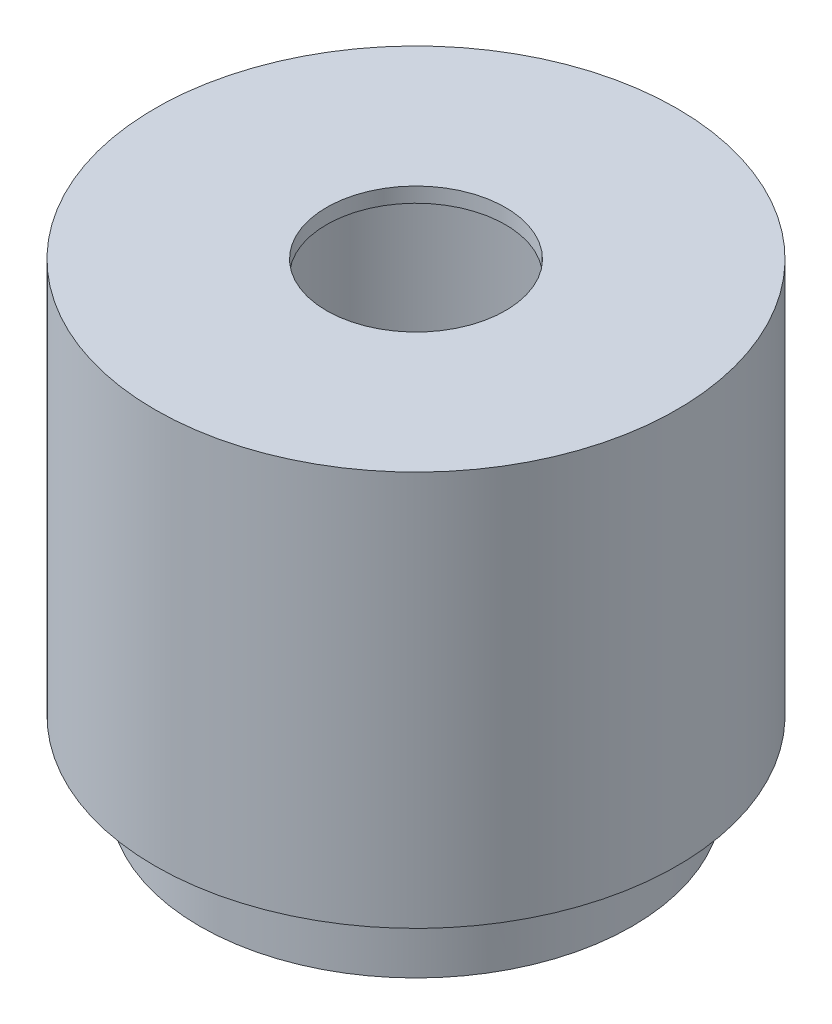
SolidWorks part; units mm, degrees
material "1060 Alloy"
ref_plane "Front Plane" through (0, 0, 0) normal (0, 0, 1) x (1, 0, 0)
ref_plane "Top Plane" through (0, 0, 0) normal (0, 1, 0) x (1, 0, 0)
ref_plane "Right Plane" through (0, 0, 0) normal (1, 0, 0) x (0, 0, -1)
sketch "Sketch1" plane through (0, 0, 0) normal (0, 1, 0) x (1, 0, 0)
  circle A0 centre (0, 0) radius 17.5
  circle A1 centre (0, 0) radius 12
  dimension "D1" = 35
  dimension "D2" = 24
extrude "Boss-Extrude1" add sketch "Sketch1" along normal blind 26.5
sketch "Sketch2" plane through (0, 26.5, 0) normal (0, 1, 0) x (1, 0, 0)
  circle A0 centre (0, 0) radius 12
  circle A1 centre (0, 0) radius 6
  dimension "D1" = 12
extrude "Boss-Extrude2" add sketch "Sketch2" against normal blind 1
sketch "Sketch3" plane through (0, 0, 0) normal (0, -1, 0) x (1, 0, 0)
  circle A0 centre (0, 0) radius 12
  circle A1 centre (0, 0) radius 14.5
  dimension "D1" = 29
extrude "Boss-Extrude3" add sketch "Sketch3" along normal blind 5
